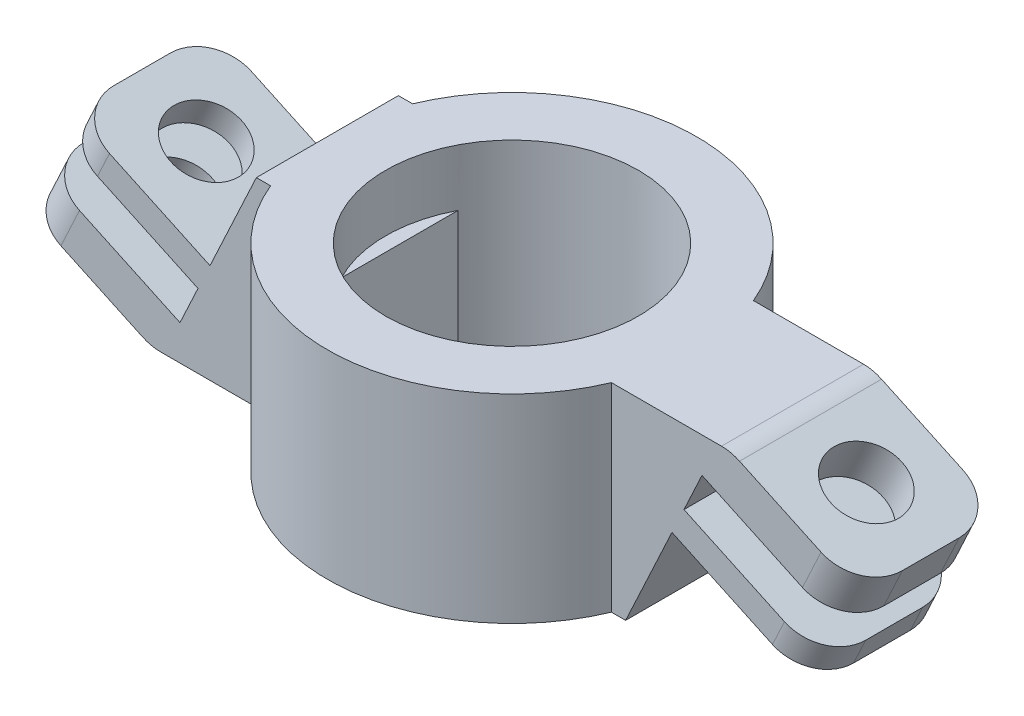
SolidWorks part; units mm, degrees
ref_plane "Front Plane" through (0, 0, 0) normal (0, 0, 1) x (1, 0, 0)
ref_plane "Top Plane" through (0, 0, 0) normal (0, 1, 0) x (1, 0, 0)
ref_plane "Right Plane" through (0, 0, 0) normal (1, 0, 0) x (0, 0, -1)
sketch "Sketch1" plane through (0, 0, 0) normal (0, 1, 0) x (1, 0, 0)
  line L2 (-3.95, 2.0494) -> (-3.95, -2.0494)
  line L3 (3.95, 2.0494) -> (3.95, -2.0494)
  line L4 (3.95, 0) -> (-3.95, 0) construction
  circle A1 centre (0, 0) radius 6.5
  arc A3 (-3.95, -2.0494) -> (3.95, -2.0494) centre (0, 0) ccw
  arc A4 (3.95, 2.0494) -> (-3.95, 2.0494) centre (0, 0) ccw
  point P9 (-3.95, 0)
  point P10 (3.95, 0)
  point P13 (0, 0)
  dimension "D3" = 13
  dimension "D1" = 8.9
  dimension "D2" = 7.9
extrude "Boss-Extrude1" add sketch "Sketch1" along normal blind 7
sketch "Sketch2" plane through (0, 0, 0) normal (0, 0, 1) x (1, 0, 0)
  line L0 (5.5, 7) -> (5.5, 0)
  line L1 (6.5, 7) -> (-6.5, 7) construction
  line L2 (-6.5, 0) -> (6.5, 0) construction
  line L3 (5.5, 0) -> (6.5, 0)
  line L4 (6.5, 0) -> (8.1321, 3.5)
  line L5 (8.1321, 3.5) -> (13.0294, 1.2164)
  line L6 (13.0294, 1.2164) -> (13.452, 2.1227)
  line L7 (13.452, 2.1227) -> (8.5547, 4.4063)
  line L8 (8.5547, 4.4063) -> (9.1886, 5.7658)
  line L9 (9.1886, 5.7658) -> (14.0859, 3.4821)
  line L10 (14.0859, 3.4821) -> (14.741, 4.8869)
  line L11 (14.741, 4.8869) -> (10.2094, 7)
  line L12 (10.2094, 7) -> (5.5, 7)
  line L15 (-5.5, 0) -> (-5.5, 7)
  line L16 (-5.5, 7) -> (-6.5, 7)
  line L17 (-6.5, 7) -> (-8.1321, 3.5)
  line L18 (-8.1321, 3.5) -> (-13.0294, 5.7836)
  line L19 (-13.0294, 5.7836) -> (-13.452, 4.8773)
  line L20 (-13.452, 4.8773) -> (-8.5547, 2.5937)
  line L21 (-8.5547, 2.5937) -> (-9.1886, 1.2342)
  line L22 (-9.1886, 1.2342) -> (-14.0859, 3.5179)
  line L23 (-14.0859, 3.5179) -> (-14.741, 2.1131)
  line L24 (-14.741, 2.1131) -> (-10.2094, 0)
  line L25 (-10.2094, 0) -> (-5.5, 0)
  line L26 (-6.5, 7) -> (-6.5, 0) construction
  point P22 (5.5, 3.5)
  point P32 (-5.5, 3.5)
  dimension "D1" = 115
  dimension "D2" = 1.5
  dimension "D3" = 1
  dimension "D4" = 1.55
  dimension "D5" = 5
  dimension "D6" = 1
  dimension "D7" = 1
  dimension "D8" = 5
  dimension "D9" = 1.5
  dimension "D10" = 1
  dimension "D11" = 1.55
  dimension "D12" = 115
extrude "Boss-Extrude2" add sketch "Sketch2" along normal mid plane 5
sketch "Sketch3" plane through (4.5046, 9.6602, 0) normal (0.4226, 0.9063, 0) x (0.9063, -0.4226, 0)
  line L0 (6.2945, 2.5) -> (11.2945, -2.5) construction
  circle A0 centre (8.7945, 0) radius 1.25
  dimension "D1" = 2.5
extrude "Cut-Extrude1" cut sketch "Sketch3" against normal through all
sketch "Sketch4" plane through (-1.8235, -3.9104, 0) normal (-0.4226, -0.9063, 0) x (0.9063, -0.4226, 0)
  line L0 (-14.2529, 2.5) -> (-9.2529, -2.5) construction
  circle A0 centre (-11.7529, 0) radius 1.25
  dimension "D1" = 2.5
extrude "Cut-Extrude2" cut sketch "Sketch4" against normal through all
fillet "Fillet1" radius 1.5 10 edges at (-14.4134, 2.8155, -2.5) (-14.4134, 2.8155, 2.5) (-13.2407, 5.3305, -2.5) (-13.2407, 5.3305, 2.5) (13.2407, 1.6695, 2.5) (13.2407, 1.6695, -2.5) (14.4134, 4.1845, -2.5) (14.4134, 4.1845, 2.5) (10.2094, 7, 0) (-10.2094, 0, 0)
sketch "Sketch5" plane through (0, 7, 0) normal (0, 1, 0) x (1, 0, 0)
  circle A0 centre (0, 0) radius 4.45
  dimension "D2" = 8.9
extrude "Cut-Extrude3" cut sketch "Sketch5" against normal blind 2
equation "\"raio interno\"=3.95"
equation "\"altura do furo\"=7"
equation "\"D1@Boss-Extrude1\"=\"altura do furo\""
equation "\"D1@Sketch1\"=\"raio interno\"*2+1"
equation "\"D2@Sketch1\"=\"raio interno\"*2"
